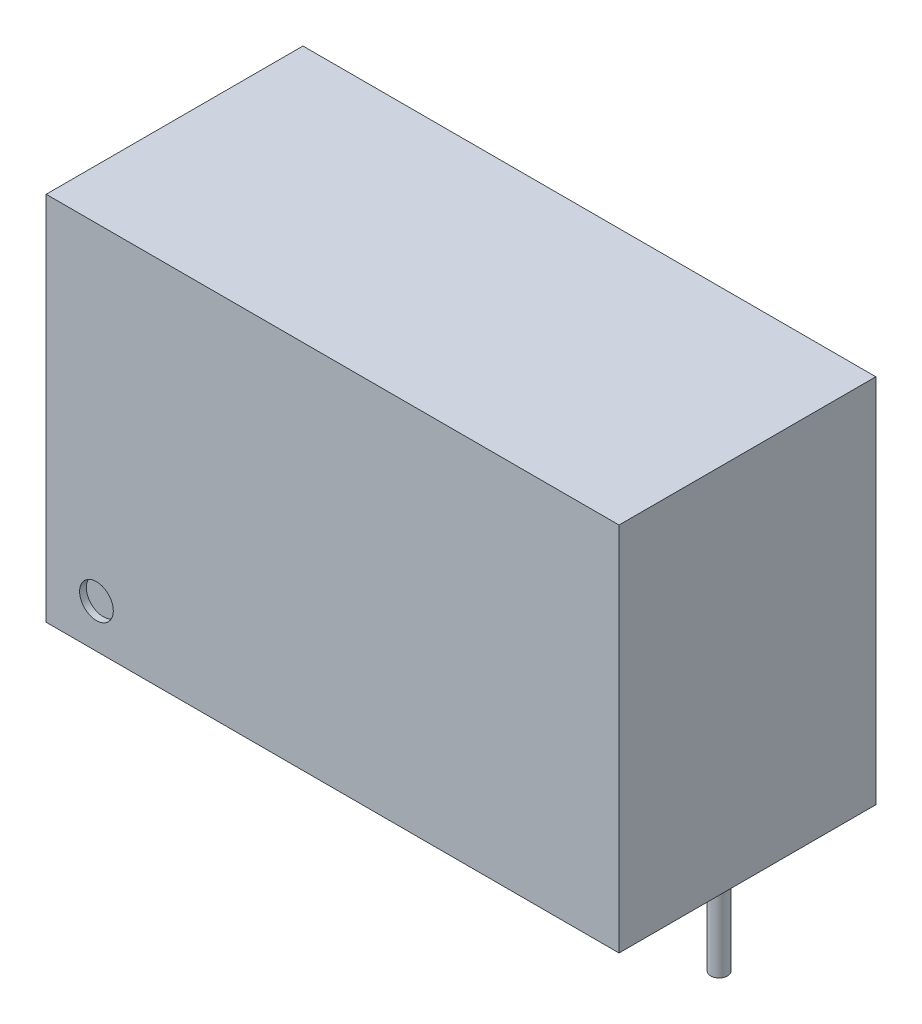
SolidWorks part; units mm, degrees
ref_plane "Front Plane" through (0, 0, 0) normal (0, 0, 1) x (1, 0, 0)
ref_plane "Top Plane" through (0, 0, 0) normal (0, 1, 0) x (1, 0, 0)
ref_plane "Right Plane" through (0, 0, 0) normal (1, 0, 0) x (0, 0, -1)
sketch "Sketch1" plane through (0, 0, 0) normal (0, 1, 0) x (1, 0, 0)
  line L1 (0, 0) -> (17, 0)
  line L2 (0, 0) -> (0, 7.62)
  line L3 (0, 7.62) -> (17, 7.62)
  line L4 (17, 0) -> (17, 7.62)
  dimension "D1" = 17
  dimension "D2" = 7.62
extrude "Boss-Extrude1" add sketch "Sketch1" along normal blind 11
sketch "Sketch2" plane through (0, 0, 0) normal (0, -1, 0) x (1, 0, 0)
  line L0 (0, -5.12) -> (17, -5.12) construction
  line L1 (0, -7.62) -> (0, 0) construction
  line L2 (17, 0) -> (17, -7.62) construction
  line L4 (17, -7.62) -> (0, -7.62) construction
  circle A0 centre (2.15, -5.12) radius 0.25
  circle A1 centre (4.69, -5.12) radius 0.25
  circle A2 centre (9.77, -5.12) radius 0.25
  circle A3 centre (12.31, -5.12) radius 0.25
  circle A4 centre (14.85, -5.12) radius 0.25
  dimension "D2" = 0.5
  dimension "D1" = 2.5
  dimension "D3" = 2.15
  dimension "D4" = 2.54
  dimension "D5" = 5.08
  dimension "D6" = 2.54
  dimension "D7" = 2.54
extrude "Boss-Extrude2" add sketch "Sketch2" along normal blind 4.1 separate body
sketch "Sketch3" plane through (0, 0, 0) normal (0, 0, 1) x (1, 0, 0)
  circle A0 centre (1.492, 1.2896) radius 0.5
  dimension "D1" = 1
extrude "Cut-Extrude1" cut sketch "Sketch3" against normal blind 0.2
